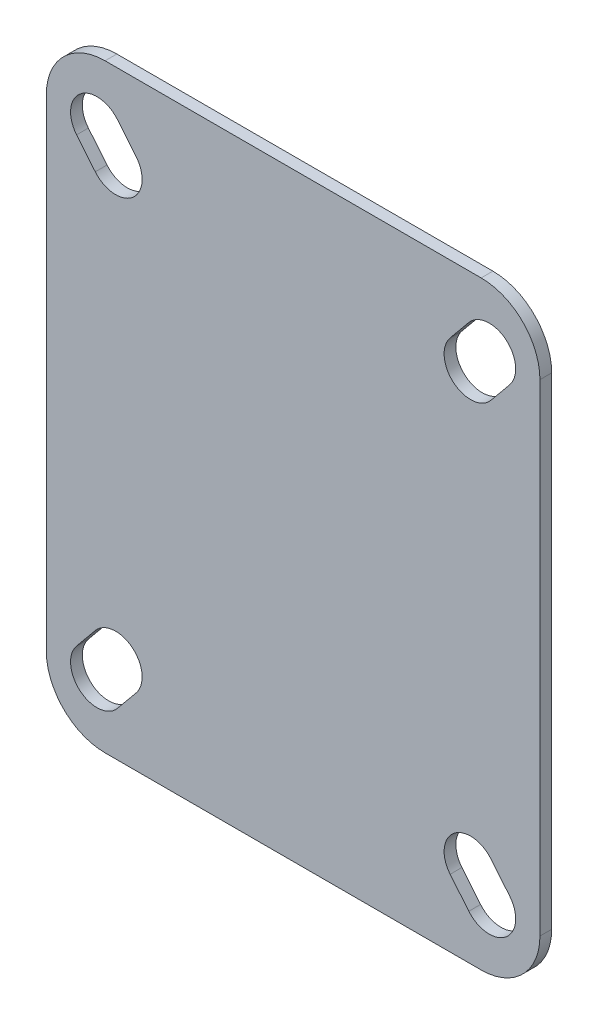
SolidWorks part; units mm, degrees
material "AISI 1020"
ref_plane "Спереди" through (0, 0, 0) normal (0, 0, 1) x (1, 0, 0)
ref_plane "Сверху" through (0, 0, 0) normal (0, 1, 0) x (1, 0, 0)
ref_plane "Справа" through (0, 0, 0) normal (1, 0, 0) x (0, 0, -1)
sketch "Эскиз1" plane through (0, 0, 0) normal (0, 0, 1) x (1, 0, 0)
  circle A0 centre (0, 27.7553) radius 27.5 construction
  circle A1 centre (0, 27.7553) radius 27.5
extrude "Бобышка-Вытянуть1" add sketch "Эскиз1" along normal blind 6 draft 16 draft outward yes
sketch "Эскиз3" plane through (0, 0, 6) normal (0, 0, 1) x (1, 0, 0)
  line L0 (-42, -23.2447) -> (42, 78.7553) construction
  line L1 (-32, 78.7553) -> (32, 78.7553)
  line L2 (-42, 68.7553) -> (-42, -13.2447)
  line L3 (-32, -23.2447) -> (32, -23.2447)
  line L4 (42, 68.7553) -> (42, -13.2447)
  line L5 (-42, 78.7553) -> (42, -23.2447) construction
  line L6 (-33.3746, 68.2816) -> (-30.1961, 64.422) construction
  line L7 (-29.9009, 71.1423) -> (-26.7224, 67.2826)
  line L8 (-36.8483, 65.4209) -> (-33.6698, 61.5613)
  line L9 (33.3746, 68.2816) -> (30.1961, 64.422) construction
  line L10 (36.8483, 65.4209) -> (33.6698, 61.5613)
  line L11 (29.9009, 71.1423) -> (26.7224, 67.2826)
  line L12 (33.3746, -12.7711) -> (30.1961, -8.9114) construction
  line L13 (29.9009, -15.6317) -> (26.7224, -11.7721)
  line L14 (36.8483, -9.9104) -> (33.6698, -6.0507)
  line L15 (-33.3746, -12.7711) -> (-30.1961, -8.9114) construction
  line L16 (-36.8483, -9.9104) -> (-33.6698, -6.0507)
  line L17 (-29.9009, -15.6317) -> (-26.7224, -11.7721)
  line L19 (-31.7854, 66.3518) -> (31.7854, 66.3518) construction
  line L20 (-31.7854, 66.3518) -> (-31.7854, -10.8412) construction
  line L21 (-31.7854, -10.8412) -> (31.7854, -10.8412) construction
  line L22 (31.7854, 66.3518) -> (31.7854, -10.8412) construction
  circle A0 centre (0, 27.7553) radius 29.2205 construction
  arc A1 (-29.9009, 71.1423) -> (-36.8483, 65.4209) centre (-33.3746, 68.2816) ccw
  arc A2 (-33.6698, 61.5613) -> (-26.7224, 67.2826) centre (-30.1961, 64.422) ccw
  arc A3 (36.8483, 65.4209) -> (29.9009, 71.1423) centre (33.3746, 68.2816) ccw
  arc A4 (26.7224, 67.2826) -> (33.6698, 61.5613) centre (30.1961, 64.422) ccw
  arc A5 (29.9009, -15.6317) -> (36.8483, -9.9104) centre (33.3746, -12.7711) ccw
  arc A6 (33.6698, -6.0507) -> (26.7224, -11.7721) centre (30.1961, -8.9114) ccw
  arc A7 (-36.8483, -9.9104) -> (-29.9009, -15.6317) centre (-33.3746, -12.7711) ccw
  arc A8 (-26.7224, -11.7721) -> (-33.6698, -6.0507) centre (-30.1961, -8.9114) ccw
  arc A9 (-32, 78.7553) -> (-42, 68.7553) centre (-32, 68.7553) ccw
  arc A10 (-42, -13.2447) -> (-32, -23.2447) centre (-32, -13.2447) ccw
  arc A11 (32, -23.2447) -> (42, -13.2447) centre (32, -13.2447) ccw
  arc A12 (32, 78.7553) -> (42, 68.7553) centre (32, 68.7553) cw
  point P4 (0, 27.7553)
  point P9 (-31.7854, 66.3518)
  point P14 (31.7854, 66.3518)
  point P21 (31.7854, -10.8412)
  point P28 (-31.7854, -10.8412)
  point P44 (-27.3354, 60.9483)
  point P45 (27.3354, -5.4377)
  dimension "D6" = 10
  dimension "D1" = 84
  dimension "D2" = 102
  dimension "D3" = 5
  dimension "D4" = 9
  dimension "D5" = 86
extrude "Бобышка-Вытянуть2" add sketch "Эскиз3" along normal blind 2
